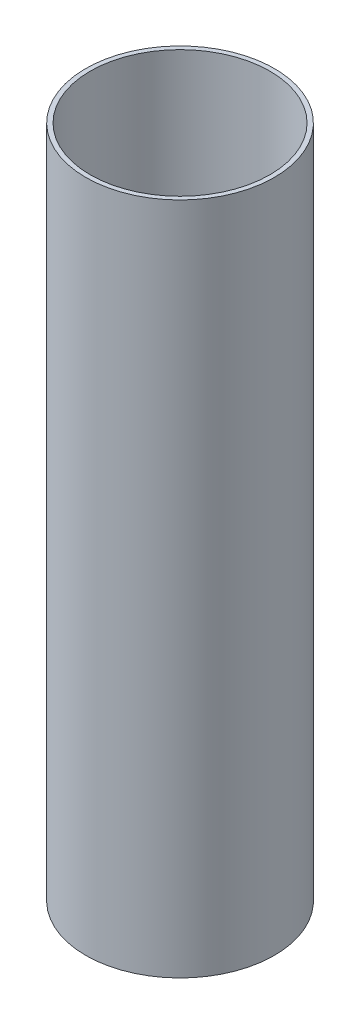
SolidWorks part; units mm, degrees
material "Acrylic (Medium-high impact)"
ref_plane "Front Plane" through (0, 0, 0) normal (0, 0, 1) x (1, 0, 0)
ref_plane "Top Plane" through (0, 0, 0) normal (0, 1, 0) x (1, 0, 0)
ref_plane "Right Plane" through (0, 0, 0) normal (1, 0, 0) x (0, 0, -1)
sketch "Sketch1" plane through (0, 0, 0) normal (0, 1, 0) x (1, 0, 0)
  circle A0 centre (0, 0) radius 38.1
  circle A1 centre (0, 0) radius 40.005
  dimension "D1" = 76.2
  dimension "D2" = 80.01
extrude "Boss-Extrude1" add sketch "Sketch1" along normal blind 285.75
